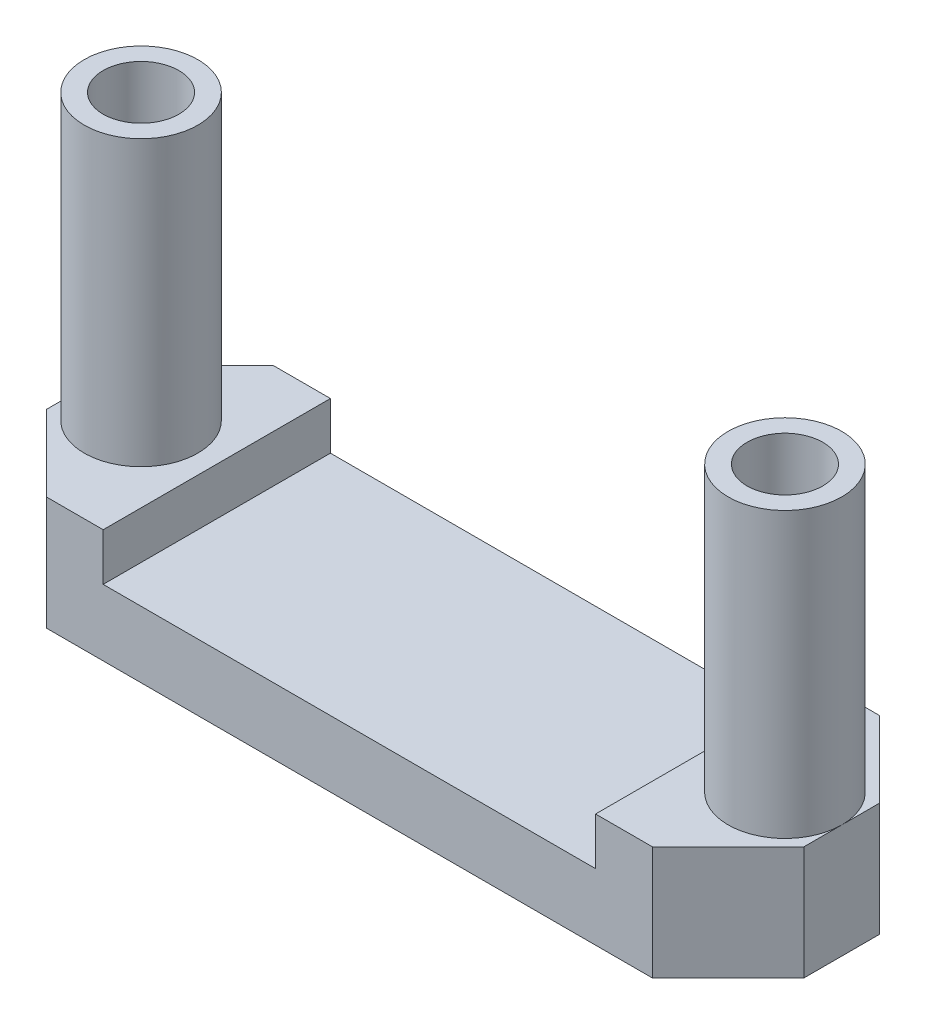
SolidWorks part; units mm, degrees
ref_plane "Front Plane" through (0, 0, 0) normal (0, 0, 1) x (1, 0, 0)
ref_plane "Top Plane" through (0, 0, 0) normal (0, 1, 0) x (1, 0, 0)
ref_plane "Right Plane" through (0, 0, 0) normal (1, 0, 0) x (0, 0, -1)
sketch "Sketch1" plane through (0, 0, 0) normal (0, 1, 0) x (1, 0, 0)
  line L0 (-10, 0) -> (10, 0) construction
  line L1 (-10, -3) -> (10, -3)
  line L2 (-10, -3) -> (-10, 3)
  line L3 (-10, 3) -> (10, 3)
  line L4 (10, -3) -> (10, 3)
  line L5 (-10, -3) -> (10, 3) construction
  line L6 (-10, 3) -> (10, -3) construction
  line L7 (0, -3) -> (0, 3) construction
  line L8 (-9.5, -3) -> (-9.5, 3) construction
  circle A0 centre (-8.5, 0) radius 1
  circle A2 centre (8.5, 0) radius 1
  point P0 (0, 0)
  dimension "D4" = 2
  dimension "D1" = 6
  dimension "D2" = 20
  dimension "D3" = 0.5
extrude "Boss-Extrude1" add sketch "Sketch1" along normal blind 3
sketch "Sketch2" plane through (0, 3, 0) normal (0, 1, 0) x (1, 0, 0)
  line L0 (10, 3) -> (-10, 3) construction
  line L1 (-6.5, -3) -> (6.5, -3)
  line L2 (-6.5, -3) -> (-6.5, 3)
  line L3 (-6.5, 3) -> (6.5, 3)
  line L4 (6.5, -3) -> (6.5, 3)
  line L5 (-6.5, -3) -> (6.5, 3) construction
  line L6 (-6.5, 3) -> (6.5, -3) construction
  point P0 (0, 0)
  dimension "D1" = 13
extrude "Cut-Extrude1" cut sketch "Sketch2" against normal blind 1.25
chamfer "Chamfer1" distance 2 angle 45 4 edges at (10, 1.5, -3) (10, 1.5, 3) (-10, 1.5, -3) (-10, 1.5, 3)
sketch "Sketch3" plane through (0, 3, 0) normal (0, 1, 0) x (1, 0, 0)
  circle A0 centre (-8.5, 0) radius 1
  circle A1 centre (-8.5, 0) radius 1.5
  circle A2 centre (-8.5, 0) radius 1 construction
  point P4 (-8.5, 1)
  point P5 (-8.5, 1)
  dimension "D1" = 0.5
extrude "Boss-Extrude2" add sketch "Sketch3" along normal blind 7.5
mirror "Mirror1" about plane through (0, 0, 0) normal (1, 0, 0) of "Boss-Extrude2"
fillet "Fillet1" [suppressed] radius 0.5
chamfer "Chamfer2" [suppressed] distance 1.25 angle 35
sketch "Sketch4" plane through (0, 1.75, 0) normal (0, 1, 0) x (1, 0, 0)
  text T0 "T"
extrude "Boss-Extrude3" [suppressed] add sketch "Sketch4" along normal blind 0.5
